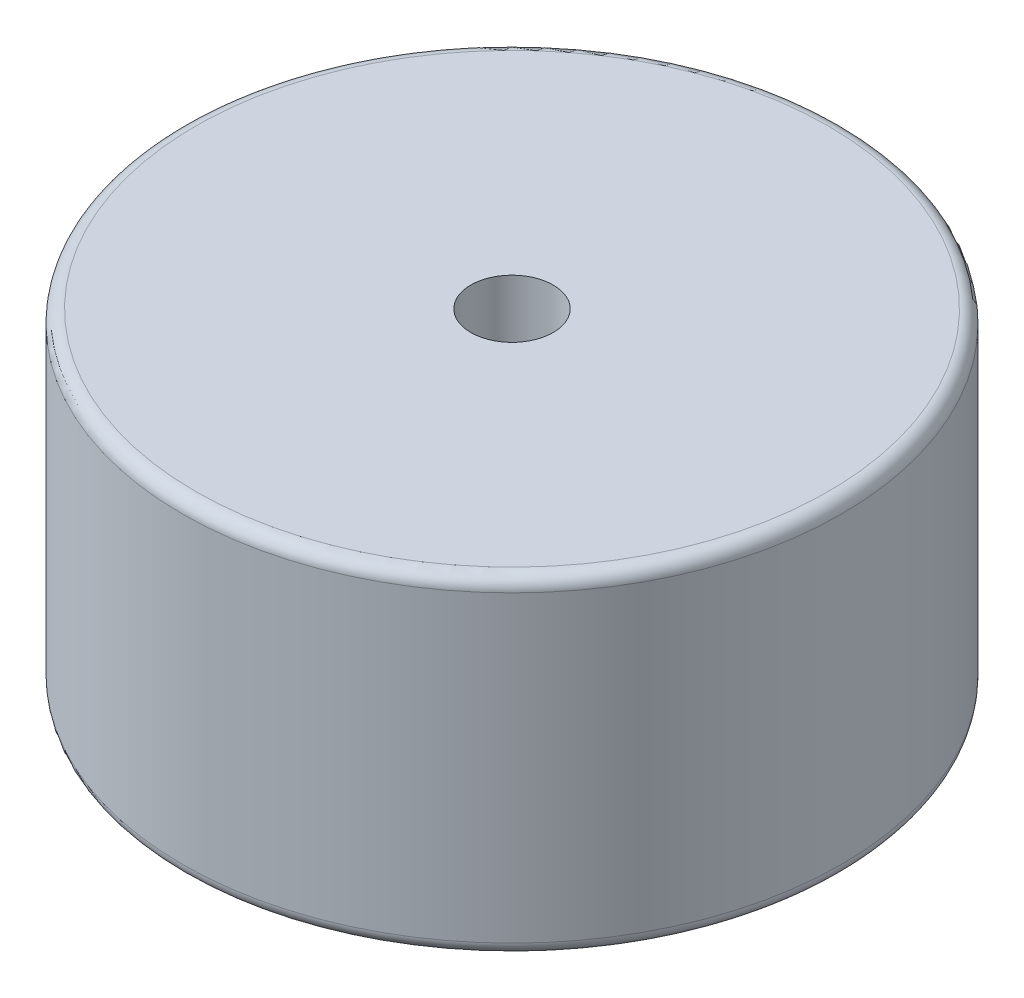
SolidWorks part; units mm, degrees
material "6061 Alloy"
ref_plane "Front" through (0, 0, 0) normal (0, 0, 1) x (1, 0, 0)
ref_plane "Top" through (0, 0, 0) normal (0, 1, 0) x (1, 0, 0)
ref_plane "Right" through (0, 0, 0) normal (1, 0, 0) x (0, 0, -1)
sketch "Sketch1" plane through (0, 0, 0) normal (0, 1, 0) x (1, 0, 0)
  circle A0 centre (0, 0) radius 20
  dimension "D1" = 40
extrude "Boss-Extrude1" add sketch "Sketch1" along normal blind 20
sketch "Sketch2" plane through (0, 20, 0) normal (0, 1, 0) x (1, 0, 0)
  circle A0 centre (0, 0) radius 2.5
  dimension "D1" = 5
extrude "Cut-Extrude1" cut sketch "Sketch2" against normal blind 12
fillet "Fillet1" radius 0.7937 2 edges at (0, 0, 20) (0, 20, 20)
sketch "Sketch3" plane through (0, 0, 0) normal (0, -1, 0) x (1, 0, 0)
  circle A0 centre (0, 0) radius 9
  circle A1 centre (0, 0) radius 17
  circle A2 centre (0, 0) radius 20 construction
  dimension "D1" = 18
  dimension "D2" = 3
extrude "Cut-Extrude2" cut sketch "Sketch3" against normal blind 0.7937 contours A1 A0
